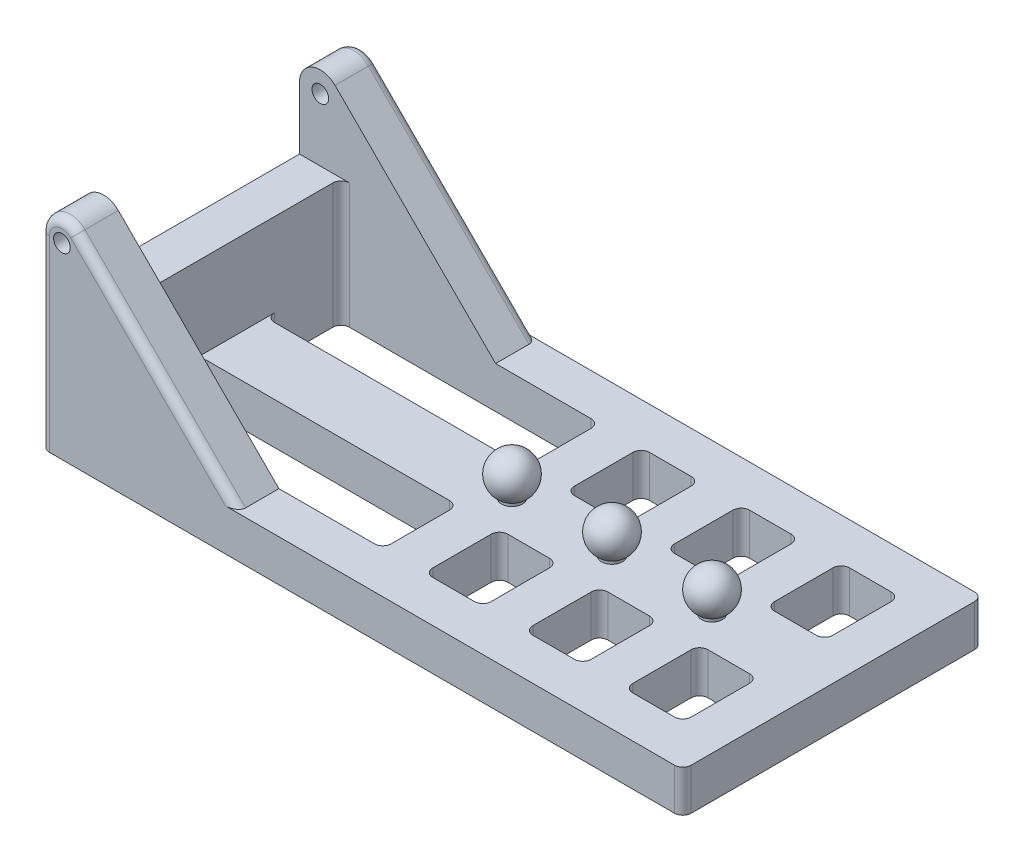
SolidWorks part; units mm, degrees
ref_plane "前视基准面" through (0, 0, 0) normal (0, 0, 1) x (1, 0, 0)
ref_plane "上视基准面" through (0, 0, 0) normal (0, 1, 0) x (1, 0, 0)
ref_plane "右视基准面" through (0, 0, 0) normal (1, 0, 0) x (0, 0, -1)
sketch "草图1" plane through (0, 0, 0) normal (0, 1, 0) x (1, 0, 0)
  line L0 (335, -130) -> (335, 130)
  line L1 (385, -180) -> (-385, -180)
  line L2 (385, -180) -> (385, 180)
  line L3 (385, 180) -> (-385, 180)
  line L4 (-385, -180) -> (-385, 180)
  line L5 (385, -180) -> (-385, 180) construction
  line L6 (385, 180) -> (-385, -180) construction
  line L7 (335, 130) -> (-335, 130)
  line L8 (-335, -130) -> (-335, 130)
  line L9 (335, -130) -> (-335, -130)
  point P0 (0, 0)
  dimension "D1" = 770
  dimension "D2" = 360
  dimension "D3" = 50
extrude "凸台-拉伸1" add sketch "草图1" along normal blind 50
sketch "草图2" plane through (0, 0, 180) normal (0, 0, 1) x (1, 0, 0)
  line L0 (-385, 50) -> (-385, 225)
  line L4 (-149.6447, 50) -> (-385, 50)
  line L5 (-360, 250) -> (-360, 50) construction
  line L6 (-342.3223, 242.6777) -> (-149.6447, 50)
  circle A0 centre (-360, 225) radius 10
  arc A1 (-342.3223, 242.6777) -> (-385, 225) centre (-360, 225) ccw
  dimension "D4" = 20
  dimension "D6" = 45
extrude "凸台-拉伸2" add sketch "草图2" against normal up to surface (50 mm away) up to face at (0, 25, 130)
sketch "草图3" plane through (0, 0, -180) normal (0, 0, -1) x (-1, 0, 0)
  line L0 (149.6447, 50) -> (385, 50)
  line L8 (342.3223, 242.6777) -> (149.6447, 50)
  line L9 (342.3223, 242.6777) -> (149.6447, 50)
  line L10 (149.6447, 50) -> (-335, 50)
  line L11 (-335, 50) -> (-335, 0)
  line L12 (-335, 0) -> (335, 0)
  line L13 (335, 0) -> (335, 50)
  line L14 (335, 50) -> (385, 50)
  line L15 (385, 50) -> (385, 225)
  line L23 (385, 50) -> (385, 225)
  circle A0 centre (360, 225) radius 10 construction
  circle A1 centre (360, 225) radius 10
  arc A2 (385, 225) -> (342.3223, 242.6777) centre (360, 225) ccw
  arc A3 (385, 225) -> (342.3223, 242.6777) centre (360, 225) ccw
  dimension "D1" = 0
extrude "凸台-拉伸3" add sketch "草图3" against normal up to surface (50 mm away) up to face at (0, 25, -130)
sketch "草图4" plane through (0, 50, 0) normal (0, 1, 0) x (1, 0, 0)
  line L0 (-335, 130) -> (-335, -130) construction
  line L1 (335, 40) -> (-335, 40)
  line L2 (335, 40) -> (335, -40)
  line L3 (335, -40) -> (-335, -40)
  line L4 (-335, 40) -> (-335, -40)
  line L5 (335, 40) -> (-335, -40) construction
  line L6 (335, -40) -> (-335, 40) construction
  point P0 (0, 0)
  dimension "D1" = 80
extrude "凸台-拉伸4" add sketch "草图4" against normal up to surface (50 mm away) up to face at (0, 0, 0)
sketch "草图8" plane through (0, 50, 0) normal (0, 1, 0) x (1, 0, 0)
  line L5 (-385, 130) -> (-335, 130)
  line L6 (-385, 130) -> (-385, -130)
  line L7 (-385, -130) -> (-335, -130)
  line L8 (-335, 130) -> (-335, -130)
extrude "凸台-拉伸6" add sketch "草图8" along normal blind 100
sketch "草图11" plane through (0, 0, 0) normal (0, 0, 1) x (1, 0, 0)
  line L0 (0, -137.5) -> (0, 137.5) construction
  line L1 (-149.6447, 50) -> (385, 50) construction
  line L2 (0, 50) -> (12.5, 50)
  line L3 (0, 50) -> (0, 99.7299)
  line L5 (12.5, 50) -> (12.5, 53.3494)
  line L6 (0, 100) -> (0, 99.7299)
  arc A0 (12.5, 53.3494) -> (0, 100) centre (0, 75) ccw
  dimension "D2" = 50
  dimension "D1" = 12.5
  dimension "D3" = 25
revolve "旋转1" add sketch "草图11" angle 360 about L3
pattern_linear "阵列(线性)27" count 3 spacing 120 along (1, 0, 0) of "旋转1"
sketch "草图12" plane through (0, 50, 0) normal (0, 1, 0) x (1, 0, 0)
  line L0 (335, 130) -> (-149.6447, 130) construction
  line L1 (-25, -130) -> (25, -130)
  line L2 (-25, -130) -> (-25, 130)
  line L3 (-25, 130) -> (25, 130)
  line L4 (25, -130) -> (25, 130)
  line L5 (-25, -130) -> (25, 130) construction
  line L6 (-25, 130) -> (25, -130) construction
  line L7 (95, -130) -> (95, 130)
  line L8 (95, -130) -> (145, -130)
  line L9 (145, -130) -> (145, 130)
  line L10 (95, 130) -> (145, 130)
  line L11 (215, -130) -> (215, 130)
  line L12 (215, -130) -> (265, -130)
  line L13 (265, -130) -> (265, 130)
  line L14 (215, 130) -> (265, 130)
  point P0 (0, 0)
  dimension "D1" = 50
  dimension "D2" = 3
extrude "凸台-拉伸10" add sketch "草图12" against normal up to surface (50 mm away) up to face at (0, 0, 85)
fillet "圆角3" radius 10 40 edges at (-335, 75, -130) (-335, 25, -40) (-335, 25, 40) (-335, 75, 130) (-25, 25, 130) (-25, 25, 40) (-25, 25, -130) (-25, 25, -40) (95, 25, -40) (25, 25, -40) (25, 25, -130) (95, 25, -130) (95, 25, 40) (95, 25, 130) (25, 25, 40) (25, 25, 130) (145, 25, -40) (145, 25, -130) (215, 25, -130) (215, 25, -40) (215, 25, 130) (215, 25, 40) (145, 25, 40) (145, 25, 130) (265, 25, 130) (265, 25, 40) (335, 25, 40) (335, 25, 130) (335, 25, -40) (265, 25, -40) (265, 25, -130) (335, 25, -130) (385, 25, -180) (385, 25, 180) (-385, 112.5, -180) (-385, 112.5, 180) (-245.9835, 146.3388, -180) (-369.5671, 248.097, -180) (-245.9835, 146.3388, 180) (-369.5671, 248.097, 180)
